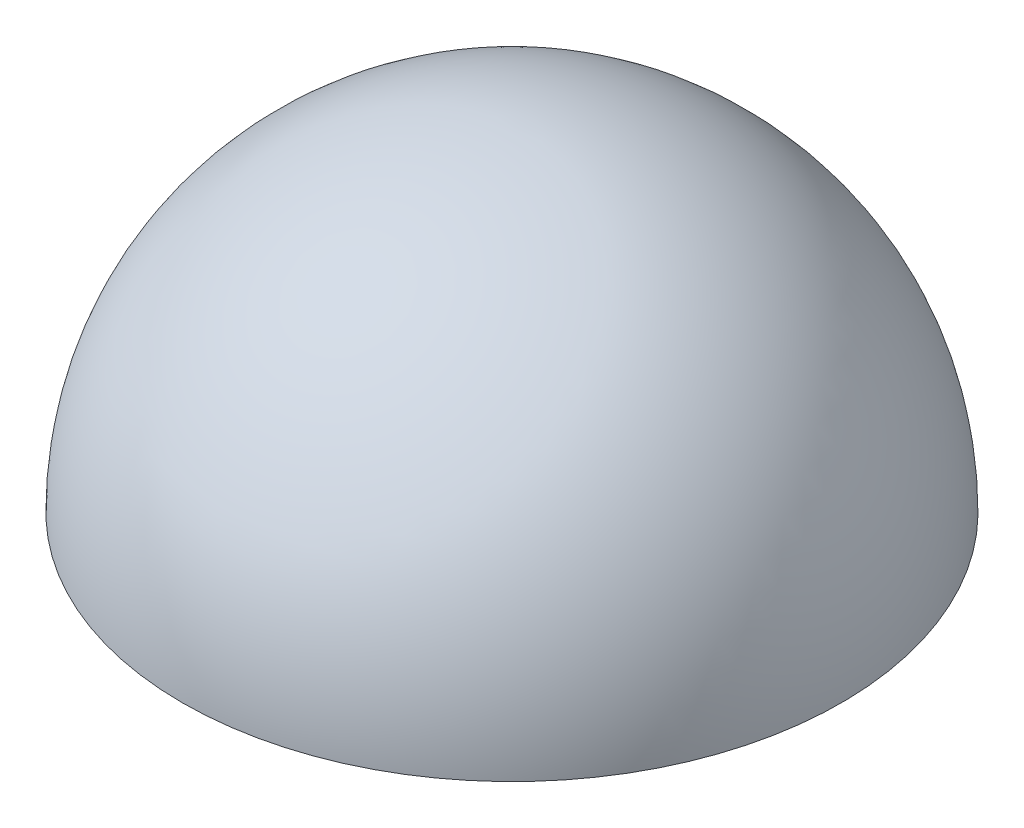
SolidWorks part; units mm, degrees
ref_plane "Front Plane" through (0, 0, 0) normal (0, 0, 1) x (1, 0, 0)
ref_plane "Top Plane" through (0, 0, 0) normal (0, 1, 0) x (1, 0, 0)
ref_plane "Right Plane" through (0, 0, 0) normal (1, 0, 0) x (0, 0, -1)
sketch "Sketch1" plane through (0, 0, 0) normal (0, 1, 0) x (1, 0, 0)
  line L0 (0, 25.25) -> (0, 23.25)
  line L1 (0, -23.25) -> (0, -25.25)
  arc A0 (0, -25.25) -> (0, 25.25) centre (0, 0) ccw
  arc A1 (0, -23.25) -> (0, 23.25) centre (0, 0) ccw
  dimension "D1" = 50.5
  dimension "D2" = 46.5
revolve "Revolve1" add sketch "Sketch1" angle 180 about L1
sketch "Sketch2" plane through (0, 0, 0) normal (0, -1, 0) x (1, 0, 0)
  circle A0 centre (0, 0) radius 24.825
  circle A1 centre (0, 0) radius 23
  dimension "D1" = 49.65
  dimension "D2" = 46
extrude "Cut-Extrude1" cut sketch "Sketch2" against normal blind 2.15
sketch "Sketch3" plane through (0, 0, 0) normal (0, -1, 0) x (1, 0, 0)
  line L0 (-5.1344, 24.2882) -> (-5, 23.6523)
  line L1 (5, 23.6523) -> (5, 24.3163)
  line L4 (23.6014, -7.6976) -> (22.9835, -7.496)
  line L5 (17.9835, -16.1563) -> (18.5585, -16.4883)
  line L6 (-18.467, -16.5907) -> (-17.9835, -16.1563)
  line L7 (-22.9835, -7.496) -> (-23.5585, -7.828)
  arc A0 (5, 24.3163) -> (-5.1344, 24.2882) centre (0, 0) ccw
  arc A1 (5, 23.6523) -> (-5, 23.6523) centre (0, 0) ccw
  arc A2 (18.5585, -16.4883) -> (23.6014, -7.6976) centre (0, 0) ccw
  arc A3 (17.9835, -16.1563) -> (22.9835, -7.496) centre (0, 0) ccw
  arc A4 (-23.5585, -7.828) -> (-18.467, -16.5907) centre (0, 0) ccw
  arc A5 (-22.9835, -7.496) -> (-17.9835, -16.1563) centre (0, 0) ccw
  point P19 (0, 0)
  dimension "D1" = 49.65
  dimension "D2" = 48.35
  dimension "D3" = 10
  dimension "D4" = 5
  dimension "D6" = 3
extrude "Boss-Extrude1" add sketch "Sketch3" against normal blind 1.05
